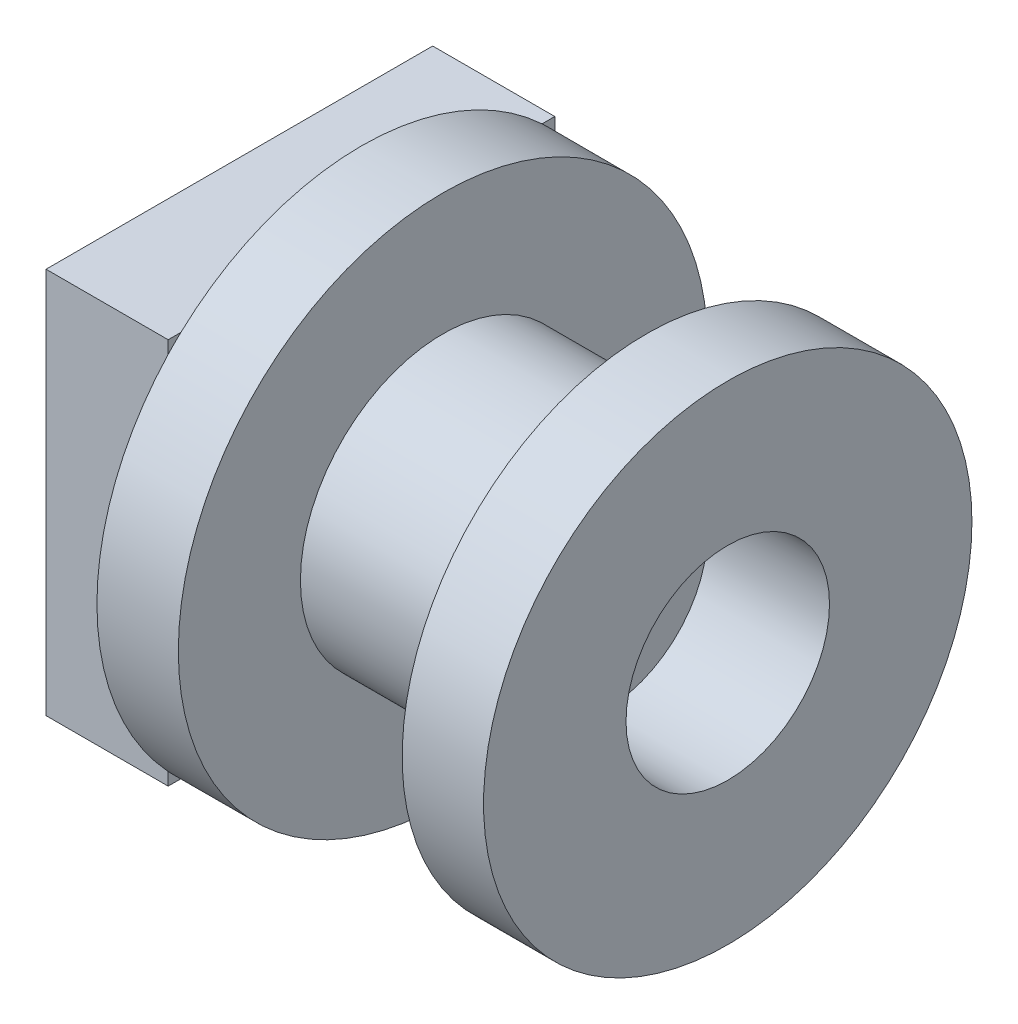
SolidWorks part; units mm, degrees
ref_plane "Front Plane" through (0, 0, 0) normal (0, 0, 1) x (1, 0, 0)
ref_plane "Top Plane" through (0, 0, 0) normal (0, 1, 0) x (1, 0, 0)
ref_plane "Right Plane" through (0, 0, 0) normal (1, 0, 0) x (0, 0, -1)
sketch "Sketch1" plane through (0, 0, 0) normal (1, 0, 0) x (0, 0, -1)
  line L1 (-1.5, -1.5) -> (1.5, -1.5)
  line L2 (-1.5, -1.5) -> (-1.5, 1.5)
  line L3 (-1.5, 1.5) -> (1.5, 1.5)
  line L4 (1.5, -1.5) -> (1.5, 1.5)
  point P5 (0, -1.5)
  point P7 (-1.5, 0)
  dimension "D1" = 3
  dimension "D2" = 3
extrude "Boss-Extrude1" add sketch "Sketch1" along normal blind 4
sketch "Sketch2" plane through (4, 0, 0) normal (1, 0, 0) x (0, 0, -1)
  line L1 (-9.5, 9.5) -> (9.5, 9.5)
  line L2 (-9.5, 9.5) -> (-9.5, -9.5)
  line L3 (-9.5, -9.5) -> (9.5, -9.5)
  line L4 (9.5, 9.5) -> (9.5, -9.5)
  point P4 (9.5, 0)
  point P6 (0, -9.5)
  dimension "D1" = 19
  dimension "D2" = 19
extrude "Boss-Extrude2" add sketch "Sketch2" along normal blind 6
sketch "Sketch3" plane through (10, 0, 0) normal (1, 0, 0) x (0, 0, -1)
  circle A0 centre (0, 0) radius 13
  dimension "D1" = 26
extrude "Boss-Extrude3" add sketch "Sketch3" along normal blind 4
sketch "Sketch4" plane through (14, 0, 0) normal (1, 0, 0) x (0, 0, -1)
  circle A0 centre (0, 0) radius 7
  dimension "D1" = 14
extrude "Boss-Extrude4" add sketch "Sketch4" along normal blind 10
sketch "Sketch5" plane through (24, 0, 0) normal (1, 0, 0) x (0, 0, -1)
  circle A0 centre (0, 0) radius 12
  dimension "D1" = 24
extrude "Boss-Extrude5" add sketch "Sketch5" along normal blind 4
sketch "Sketch6" plane through (28, 0, 0) normal (1, 0, 0) x (0, 0, -1)
  circle A0 centre (0, 0) radius 5
  dimension "D1" = 10
extrude "Cut-Extrude1" cut sketch "Sketch6" against normal blind 6
